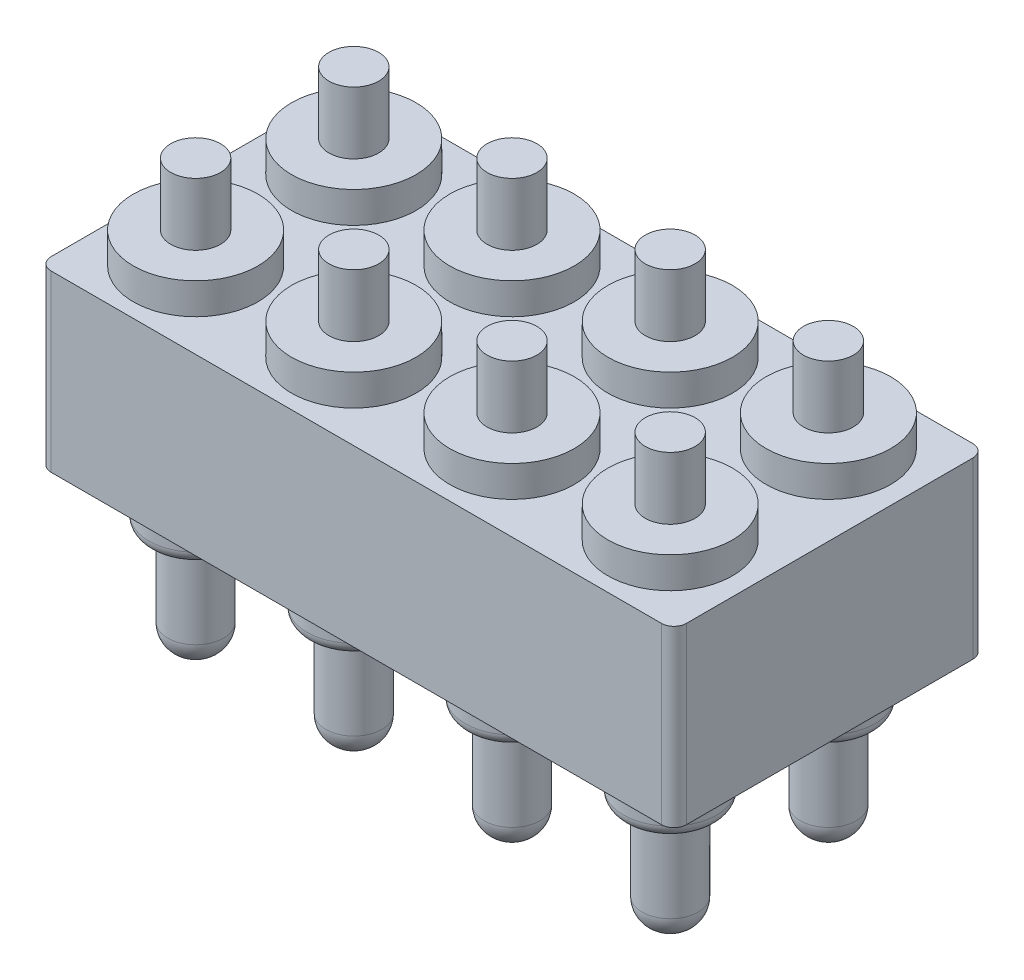
SolidWorks part; units mm, degrees
ref_plane "前视基准面" through (0, 0, 0) normal (0, 0, 1) x (1, 0, 0)
ref_plane "上视基准面" through (0, 0, 0) normal (0, 1, 0) x (1, 0, 0)
ref_plane "右视基准面" through (0, 0, 0) normal (1, 0, 0) x (0, 0, -1)
sketch "草图1" plane through (0, 0, 0) normal (0, 1, 0) x (1, 0, 0)
  line L1 (0, 0) -> (10.2, 0)
  line L2 (0, 0) -> (0, 5)
  line L3 (0, 5) -> (10.2, 5)
  line L4 (10.2, 0) -> (10.2, 5)
  dimension "D1" = 10.2
  dimension "D2" = 5
extrude "凸台-拉伸1" add sketch "草图1" along normal blind 2.8
sketch "草图2" plane through (0, 2.8, 0) normal (0, 1, 0) x (1, 0, 0)
  line L0 (-1.5872, 2.5) -> (11.8991, 2.5) construction
  line L1 (5.1, 7.4834) -> (5.1, -2.5154) construction
  circle A0 centre (1.29, 3.77) radius 0.75
  circle A1 centre (3.83, 3.77) radius 0.75
  circle A2 centre (6.37, 3.77) radius 0.75
  circle A3 centre (8.91, 3.77) radius 0.75
  circle A4 centre (3.83, 1.23) radius 0.75
  circle A5 centre (6.37, 1.23) radius 0.75
  circle A6 centre (8.91, 1.23) radius 0.75
  circle A7 centre (1.29, 1.23) radius 0.75
  dimension "D1" = 1.5
  dimension "D2" = 3.81
  dimension "D3" = 1.27
  dimension "D4" = 2
extrude "凸台-拉伸2" add sketch "草图2" against normal blind 3.65
sketch "草图3" plane through (0, 2.8, 0) normal (0, 1, 0) x (1, 0, 0)
  line L0 (1.29, 3.77) -> (1.29, -0.6334) construction
  circle A0 centre (1.29, 3.77) radius 1
  circle A1 centre (3.83, 3.77) radius 1
  circle A3 centre (1.29, 3.77) radius 0.75
  circle A4 centre (1.29, 3.77) radius 0.75 construction
  circle A5 centre (6.37, 3.77) radius 1
  circle A6 centre (8.91, 3.77) radius 1
  circle A7 centre (3.83, 1.23) radius 1
  circle A8 centre (6.37, 1.23) radius 1
  circle A9 centre (8.91, 1.23) radius 1
  circle A10 centre (1.29, 1.23) radius 1
  dimension "D1" = 2
  dimension "D2" = 0
  dimension "D3" = 2
extrude "凸台-拉伸3" add sketch "草图3" along normal blind 0.5
sketch "草图4" plane through (0, 3.3, 0) normal (0, 1, 0) x (1, 0, 0)
  circle A0 centre (1.29, 1.23) radius 0.4
  circle A1 centre (3.83, 1.23) radius 0.4
  circle A2 centre (6.37, 1.23) radius 0.4
  circle A3 centre (8.91, 1.23) radius 0.4
  circle A4 centre (3.83, 3.77) radius 0.4
  circle A5 centre (6.37, 3.77) radius 0.4
  circle A6 centre (8.91, 3.77) radius 0.4
  circle A7 centre (1.29, 3.77) radius 0.4
  dimension "D1" = 0.8
  dimension "D2" = 2
extrude "凸台-拉伸4" add sketch "草图4" along normal blind 1
sketch "草图5" plane through (0, -0.85, 0) normal (0, -1, 0) x (1, 0, 0)
  circle A0 centre (1.29, -3.77) radius 0.45
  circle A1 centre (3.83, -3.77) radius 0.45
  circle A2 centre (6.37, -3.77) radius 0.45
  circle A3 centre (8.91, -3.77) radius 0.45
  circle A4 centre (3.83, -1.23) radius 0.45
  circle A5 centre (6.37, -1.23) radius 0.45
  circle A6 centre (8.91, -1.23) radius 0.45
  circle A7 centre (1.29, -1.23) radius 0.45
  dimension "D1" = 0.9
  dimension "D2" = 2
extrude "凸台-拉伸5" add sketch "草图5" along normal blind 1.7
fillet "圆角1" radius 0.2 8 edges at (8.91, -0.85, -0.48) (6.37, -0.85, -0.48) (3.83, -0.85, -0.48) (1.29, -0.85, -0.48) (1.29, -0.85, -3.02) (3.83, -0.85, -3.02) (6.37, -0.85, -3.02) (8.91, -0.85, -3.02)
fillet "圆角2" radius 0.4 8 edges at (8.91, -2.55, -1.68) (6.37, -2.55, -1.68) (3.83, -2.55, -1.68) (1.29, -2.55, -1.68) (1.29, -2.55, -4.22) (3.83, -2.55, -4.22) (6.37, -2.55, -4.22) (8.91, -2.55, -4.22)
fillet "圆角3" radius 0.2 4 edges at (0, 1.4, -5) (10.2, 1.4, -5) (10.2, 1.4, 0) (0, 1.4, 0)
